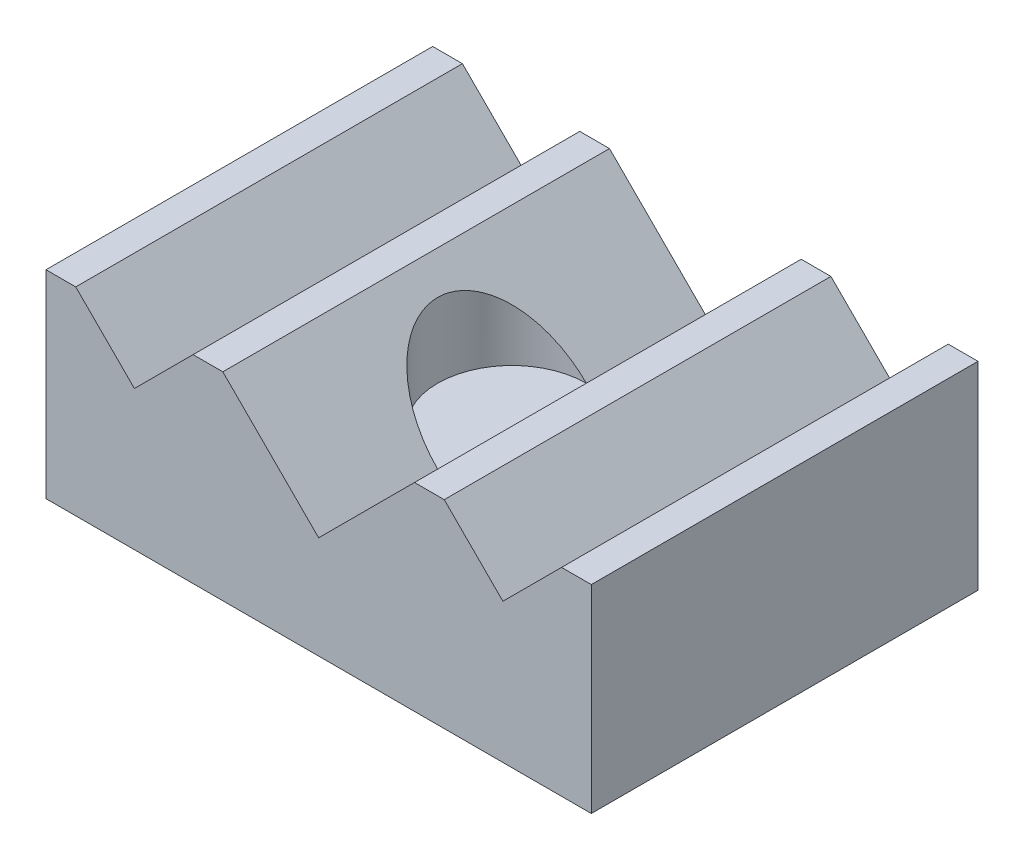
SolidWorks part; units mm, degrees
material "Rubber"
ref_plane "Front Plane" through (0, 0, 0) normal (0, 0, 1) x (1, 0, 0)
ref_plane "Top Plane" through (0, 0, 0) normal (0, 1, 0) x (1, 0, 0)
ref_plane "Right Plane" through (0, 0, 0) normal (1, 0, 0) x (0, 0, -1)
sketch "Sketch1" plane through (0, 0, 0) normal (0, 1, 0) x (1, 0, 0)
  line L1 (0, 0) -> (20.955, 0)
  line L2 (0, 0) -> (0, 14.859)
  line L3 (0, 14.859) -> (20.955, 14.859)
  line L4 (20.955, 0) -> (20.955, 14.859)
  dimension "D1" = 20.955
  dimension "D2" = 14.859
extrude "Boss-Extrude1" add sketch "Sketch1" along normal blind 7.62
sketch "Sketch2" plane through (0, 0, 0) normal (0, 0, 1) x (1, 0, 0)
  line L0 (0, 7.62) -> (1.143, 7.62)
  line L1 (0, 7.62) -> (20.955, 7.62) construction
  line L2 (1.143, 7.62) -> (3.3973, 5.3658)
  line L3 (3.3973, 5.3658) -> (5.6515, 7.62)
  line L4 (5.6515, 7.62) -> (6.7945, 7.62)
  line L5 (6.7945, 7.62) -> (10.4775, 3.937)
  line L6 (10.4775, 3.937) -> (14.1605, 7.62)
  line L7 (14.1605, 7.62) -> (15.3035, 7.62)
  line L8 (15.3035, 7.62) -> (17.5577, 5.3658)
  line L9 (17.5577, 5.3658) -> (19.812, 7.62)
  line L10 (19.812, 7.62) -> (20.955, 7.62)
  line L11 (1.143, 7.62) -> (19.812, 7.62)
  line M13 (20.955, 7.62) -> (0, 7.62)
  dimension "D1" = 1.143
  dimension "D2" = 3.683
extrude "Cut-Extrude1" cut sketch "Sketch2" against normal through all contours L2 L3 M13 | L5 L6 M13 | L8 L9 M13
ref_plane "Plane1" through (0, 3.937, 0) normal (0, 1, 0) x (1, 0, 0)
sketch "Sketch3" plane through (0, 3.937, 0) normal (0, 1, 0) x (1, 0, 0)
  line L0 (10.4775, 14.859) -> (10.4775, 0) construction
  line L1 (10.4775, 14.859) -> (10.4775, 0) construction
  circle A0 centre (10.4775, 7.4295) radius 2.8575
  point P4 (0, 0)
  point P5 (0, 0)
  dimension "D1" = 5.715
extrude "Cut-Extrude2" cut sketch "Sketch3" along normal through all
sketch "Sketch4" plane through (0, 0, 0) normal (0, -1, 0) x (1, 0, 0)
  line L0 (10.4775, 0) -> (10.4775, -14.859) construction
  line L1 (0, -7.4295) -> (20.955, -7.4295) construction
  line L2 (3.1115, -3.7846) -> (17.8435, -3.7846) construction
  line L3 (16.9164, -2.8575) -> (16.9164, -12.0015) construction
  line L4 (0, 0) -> (0, -14.859)
  line L5 (0, -14.859) -> (20.955, -14.859)
  line L6 (20.955, -14.859) -> (20.955, 0)
  line L7 (20.955, 0) -> (0, 0)
  line L8 (0, 0) -> (0, -14.859)
  line L9 (0, -14.859) -> (20.955, -14.859)
  line L10 (20.955, -14.859) -> (20.955, 0)
  line L11 (20.955, 0) -> (0, 0)
  circle A0 centre (4.0386, -3.7846) radius 0.9271
  circle A1 centre (16.9164, -3.7846) radius 0.9271
  circle A2 centre (16.9164, -11.0744) radius 0.9271
  circle A3 centre (4.0386, -11.0744) radius 0.9271
  circle A4 centre (10.4775, -7.4295) radius 0.9271
  point P22 (10.4775, -3.7846)
  point P23 (16.9164, -7.4295)
  point P24 (0, 0)
  point P25 (0, 0)
  dimension "D2" = 1.8542
  dimension "D3" = 14.732
  dimension "D4" = 9.144
  dimension "D1" = 0
extrude "Cut-Extrude3" cut sketch "Sketch4" against normal blind 3.81 contours A0 | A3 | A4 | A2 | A1
